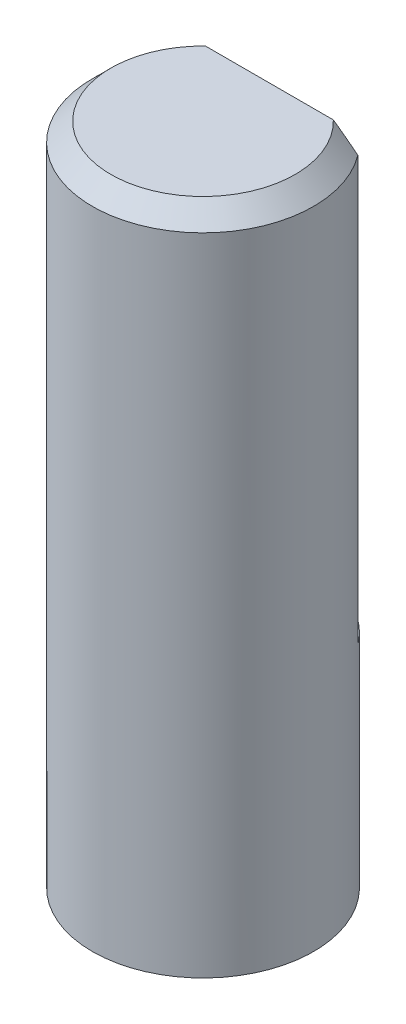
SolidWorks part; units mm, degrees
ref_plane "Спереди" through (0, 0, 0) normal (0, 0, 1) x (1, 0, 0)
ref_plane "Сверху" through (0, 0, 0) normal (0, 1, 0) x (1, 0, 0)
ref_plane "Справа" through (0, 0, 0) normal (1, 0, 0) x (0, 0, -1)
sketch "Эскиз1" plane through (0, 0, 0) normal (0, 1, 0) x (1, 0, 0)
  circle A1 centre (0, 0) radius 3
extrude "Бобышка-Вытянуть1" add sketch "Эскиз1" along normal blind 18
chamfer "Фаска1" distance 0.5 angle 45 1 edges at (0, 18, 3)
sketch "Эскиз2" plane through (0, 18, 0) normal (0, 1, 0) x (1, 0, 0)
  line L0 (-2.4, 1.8) -> (2.4, 1.8)
  arc A0 (2.4, 1.8) -> (-2.4, 1.8) centre (0, 0) ccw
  dimension "D1" = 1.8
  dimension "D2" = 6
extrude "Вырез-Вытянуть1" cut sketch "Эскиз2" against normal blind 12 contours L0 A0
